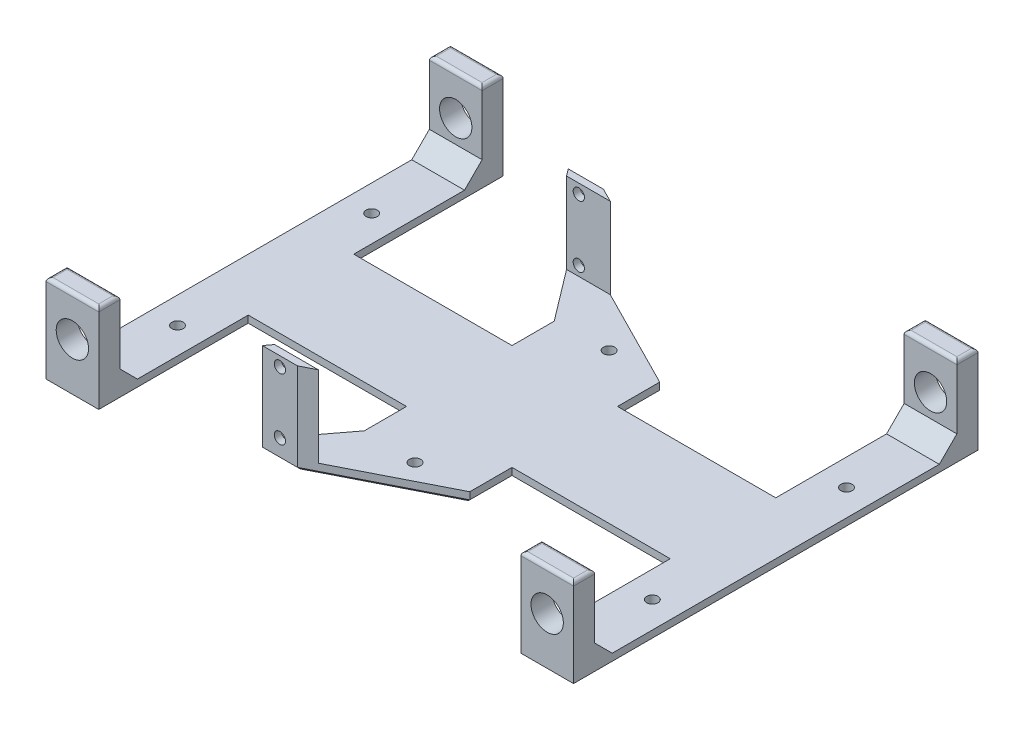
SolidWorks part; units mm, degrees
ref_plane "Front Plane" through (0, 0, 0) normal (0, 0, 1) x (1, 0, 0)
ref_plane "Top Plane" through (0, 0, 0) normal (0, 1, 0) x (1, 0, 0)
ref_plane "Right Plane" through (0, 0, 0) normal (1, 0, 0) x (0, 0, -1)
sketch "Sketch1" plane through (0, 0, 0) normal (0, 1, 0) x (1, 0, 0)
  line L0 (-67.5, 0) -> (67.5, 0) construction
  line L1 (-70, 25) -> (70, 25) construction
  line L2 (-70, 25) -> (-70, -25) construction
  line L3 (-70, -25) -> (70, -25) construction
  line L4 (70, 25) -> (70, -25) construction
  line L5 (-70, 25) -> (70, -25) construction
  line L6 (-70, -25) -> (70, 25) construction
  line L7 (-15, 27) -> (15, 27)
  line L8 (-15, 27) -> (-15, -27)
  line L9 (-15, -27) -> (15, -27)
  line L10 (15, 27) -> (15, -27)
  line L11 (-15, 27) -> (15, -27) construction
  line L12 (-15, -27) -> (15, 27) construction
  line L13 (-75, 57.5) -> (-75, -57.5)
  line L14 (-75, 27) -> (-60, 27)
  line L15 (-75, 27) -> (-75, -27)
  line L16 (-75, -27) -> (-60, -27)
  line L17 (-60, 27) -> (-60, -27)
  line L18 (-75, 27) -> (-60, -27) construction
  line L19 (-75, -27) -> (-60, 27) construction
  line L20 (-75, 51.5) -> (-60, 51.5)
  line L21 (-27.5, 43.5) -> (-17.5, 43.5)
  line L22 (-22.5, 73.5) -> (-22.5, 48.1057) construction
  line L23 (-27.5, 43.5) -> (-15, 27)
  line L24 (-17.5, 43.5) -> (15, 27)
  line L26 (-75, 57.5) -> (-60, 57.5)
  line L27 (-60, 57.5) -> (-60, 27)
  point P0 (0, 0)
  point P5 (0, 0)
  point P23 (-75, 0)
  point P27 (-22.5, 43.5)
  dimension "D1" = 50
  dimension "D2" = 140
  dimension "D3" = 54
  dimension "D4" = 135
  dimension "D5" = 5
  dimension "D6" = 30
  dimension "D7" = 6
  dimension "D8" = 115
  dimension "D9" = 14
  dimension "D10" = 45
  dimension "D11" = 10
sketch "Sketch2" plane through (0, 0, 0) normal (0, 1, 0) x (1, 0, 0)
  line L0 (-75, 57.5) -> (-60, 57.5) construction
  line L1 (-75, 57.5) -> (-75, -57.5) construction
  line L2 (-75, 51.5) -> (-60, 51.5) construction
  line L3 (-60, 57.5) -> (-60, 27) construction
  line L4 (-75, 27) -> (-60, 27) construction
  line L5 (-60, 27) -> (-60, -27) construction
  line L6 (-75, -27) -> (-60, -27) construction
  line L7 (-15, 27) -> (-15, -27) construction
  line L8 (-15, -27) -> (15, -27) construction
  line L9 (15, 27) -> (15, -27) construction
  line L10 (-15, 27) -> (15, 27) construction
  line L11 (-27.5, 43.5) -> (-15, 27) construction
  line L12 (-27.5, 43.5) -> (-17.5, 43.5) construction
  line L13 (-17.5, 43.5) -> (15, 27) construction
  line L14 (-75, 57.5) -> (-60, 57.5)
  line L15 (-75, 57.5) -> (-75, -57.5)
  line L16 (-75, 51.5) -> (-60, 51.5) construction
  line L17 (-60, 57.5) -> (-60, 27)
  line L18 (-75, 27) -> (-60, 27) construction
  line L19 (-60, 27) -> (-60, -27)
  line L20 (-75, -27) -> (-60, -27)
  line L21 (-15, 27) -> (-15, -27)
  line L22 (-15, -27) -> (15, -27)
  line L23 (15, 27) -> (15, -27)
  line L24 (-15, 27) -> (15, 27) construction
  line L25 (-27.5, 43.5) -> (-15, 27)
  line L26 (-27.5, 43.5) -> (-17.5, 43.5)
  line L27 (-17.5, 43.5) -> (15, 27)
  line L28 (0, 25) -> (0, -25) construction
  line L29 (-70, 25) -> (70, 25) construction
  line L30 (-70, -25) -> (70, -25) construction
  line L31 (-67.5, 0) -> (67.5, 0) construction
  line L32 (-67.5, 0) -> (67.5, 0) construction
  line L33 (75, -27) -> (60, -27)
  line L34 (75, 57.5) -> (60, 57.5)
  line L35 (60, 57.5) -> (60, 27)
  line L36 (75, 57.5) -> (75, -57.5)
  line L37 (60, 27) -> (60, -27)
  line L38 (75, -57.5) -> (60, -57.5)
  line L39 (60, -57.5) -> (60, -27)
  line L40 (-75, -57.5) -> (-60, -57.5)
  line L41 (-60, -57.5) -> (-60, -27)
  line L42 (-17.5, -43.5) -> (15, -27)
  line L43 (-27.5, -43.5) -> (-15, -27)
  line L44 (-27.5, -43.5) -> (-17.5, -43.5)
  line L46 (-67.5, 15) -> (67.5, 15)
  line L47 (-67.5, 15) -> (-67.5, -15)
  line L48 (-67.5, -15) -> (67.5, -15)
  line L49 (67.5, 15) -> (67.5, -15)
  line L50 (-67.5, 15) -> (67.5, -15) construction
  line L51 (-67.5, -15) -> (67.5, 15) construction
  point P33 (0, 0)
  dimension "D1" = 30
extrude "Boss-Extrude1" add sketch "Sketch2" along normal blind 3 contours L40 L41 L20 L15 | L48 L47 L46 L19 L17 L14 L15 L20 | L47 L48 L19 L46 | L19 L48 L21 L46 | L21 L48 L23 L46 | L21 L46 L23 L27 L26 L25 | L43 L44 L42 L22 | L48 L21 L22 L23 | L23 L48 L37 L46 | L49 L46 L37 L48 | L46 L49 L48 L37 L33 L36 L34 L35 | L39 L38 L36 L33
sketch "Sketch3" plane through (0, 3, 0) normal (0, 1, 0) x (1, 0, 0)
  line L0 (-75, 57.5) -> (-60, 57.5) construction
  line L1 (-75, 51.5) -> (-60, 51.5) construction
  line L2 (-75, 57.5) -> (-75, -57.5) construction
  line L3 (-60, 57.5) -> (-60, 27) construction
  line L4 (-27.5, 43.5) -> (-17.5, 43.5) construction
  line L5 (-27.5, 43.5) -> (-15, 27) construction
  line L6 (-17.5, 43.5) -> (15, 27) construction
  line L7 (-75, 57.5) -> (-60, 57.5)
  line L8 (-75, 51.5) -> (-60, 51.5)
  line L9 (-75, 57.5) -> (-75, -57.5)
  line L10 (-60, 57.5) -> (-60, 27)
  line L11 (-27.5, 43.5) -> (-17.5, 43.5)
  line L12 (-27.5, 43.5) -> (-15, 27)
  line L13 (-17.5, 43.5) -> (15, 27)
  line L14 (-25.9848, 41.5) -> (-13.5606, 41.5)
  line L15 (0, 0) -> (0, 64.6874) construction
  line L16 (60, 57.5) -> (60, 27)
  line L17 (75, 57.5) -> (75, -57.5)
  line L18 (75, 51.5) -> (60, 51.5)
  line L19 (75, 57.5) -> (60, 57.5)
  line M12 (75, 57.5) -> (60, 57.5)
  line M13 (60, 57.5) -> (60, 15)
  line M17 (-17.5, 43.5) -> (-27.5, 43.5)
  line M18 (-27.5, 43.5) -> (-15, 27)
  line M21 (-60, 15) -> (-60, 57.5)
  line M22 (-60, 57.5) -> (-75, 57.5)
  line M23 (-75, 57.5) -> (-75, -57.5)
  dimension "D1" = 2
extrude "Boss-Extrude2" add sketch "Sketch3" along normal blind 23 contours L8 M23 M21 M22 | L14 L13 M18 M17 | L18 L17 M12 M13
sketch "Sketch4" plane through (0, 0, -43.5) normal (0, 0, -1) x (-1, 0, 0)
  line L0 (22.5, 3) -> (22.5, 26) construction
  line L1 (17.5, 26) -> (27.5, 26) construction
  line L2 (22.5, 14.5) -> (10.7403, 14.5) construction
  circle A0 centre (22.5, 23.25) radius 1.6
  circle A1 centre (22.5, 5.75) radius 1.6
  dimension "D1" = 3.2
  dimension "D2" = 3
  dimension "D3" = 8.75
extrude "Cut-Extrude1" cut sketch "Sketch4" against normal blind 23
sketch "Sketch5" plane through (0, 0, -57.5) normal (0, 0, -1) x (-1, 0, 0)
  line L0 (67.5, 3) -> (67.5, 26) construction
  line L2 (60, 26) -> (75, 26) construction
  line L3 (75, 0) -> (60, 0) construction
  circle A0 centre (67.5, 14.5) radius 4.6
  dimension "D2" = 9.2
  dimension "D1" = 3
extrude "Cut-Extrude2" cut sketch "Sketch5" against normal blind 23
mirror "Mirror3" about plane through (0, 0, 0) normal (1, 0, 0) of "Cut-Extrude2"
mirror "Mirror4" about plane through (0, 0, 0) normal (0, 0, 1) of bodies 105
sketch "Sketch6" plane through (0, 3, 0) normal (0, 1, 0) x (1, 0, 0)
  line L0 (-70, 25) -> (70, 25) construction
  line L1 (0, 0) -> (0, 20.5507) construction
  line L2 (-67.5, 0) -> (67.5, 0) construction
  line L3 (-67.5, 0) -> (67.5, 0)
  circle A0 centre (-67.5, 27.6) radius 1.6
  circle A1 centre (0, 27.6) radius 1.6
  circle A2 centre (67.5, 27.6) radius 1.6
  circle A3 centre (67.5, -27.6) radius 1.6
  circle A4 centre (0, -27.6) radius 1.6
  circle A5 centre (-67.5, -27.6) radius 1.6
  dimension "D1" = 3.2
  dimension "D2" = 3.2
  dimension "D3" = 2.6
extrude "Cut-Extrude3" cut sketch "Sketch6" against normal blind 23 contours A0 | A1 | A2 | A3 | A5 | A4
chamfer "Chamfer1" distance 1 angle 45 24 edges at (-67.5, 0, 57.5) (-37.5, 0, 15) (-15, 0, 21) (-21.25, 0, 35.25) (-22.5, 0, 43.5) (-1.25, 0, 35.25) (15, 0, 21) (37.5, 0, 15) (60, 0, 36.25) (67.5, 0, 57.5) (75, 0, 0) (67.5, 0, -57.5) (60, 0, -36.25) (37.5, 0, -15) (15, 0, -21) (-1.25, 0, -35.25) (-22.5, 0, -43.5) (-21.25, 0, -35.25) (-15, 0, -21) (-37.5, 0, -15) (-60, 0, -36.25) (-67.5, 0, -57.5) (-75, 0, 0) (-60, 0, 36.25)
fillet "Fillet1" radius 1 16 edges at (60, 26, 54.5) (75, 26, 54.5) (67.5, 26, 51.5) (67.5, 26, 57.5) (75, 26, -54.5) (60, 26, -54.5) (67.5, 26, -51.5) (67.5, 26, -57.5) (-67.5, 26, -57.5) (-60, 26, -54.5) (-67.5, 26, -51.5) (-75, 26, -54.5) (-75, 26, 54.5) (-60, 26, 54.5) (-67.5, 26, 51.5) (-67.5, 26, 57.5)
sketch "Sketch7" plane through (0, 0, 0) normal (0, 1, 0) x (1, 0, 0)
  line L1 (-78.3123, -40.4384) -> (-51.524, -40.4384)
  line L2 (-78.3123, -40.4384) -> (-78.3123, -63.0409)
  line L3 (-78.3123, -63.0409) -> (-51.524, -63.0409)
  line L4 (-51.524, -40.4384) -> (-51.524, -63.0409)
  line L5 (-97.9445, 75.2696) -> (91.2474, 75.2696)
  line L6 (-97.9445, 75.2696) -> (-97.9445, -75.4783)
  line L7 (-97.9445, -75.4783) -> (91.2474, -75.4783)
  line L8 (91.2474, 75.2696) -> (91.2474, -75.4783)
extrude "Cut-Extrude4" [suppressed] cut sketch "Sketch7" along normal through all
chamfer "Chamfer2" distance 5 angle 45 4 edges at (67.5, 3, 51.5) (67.5, 3, -51.5)
